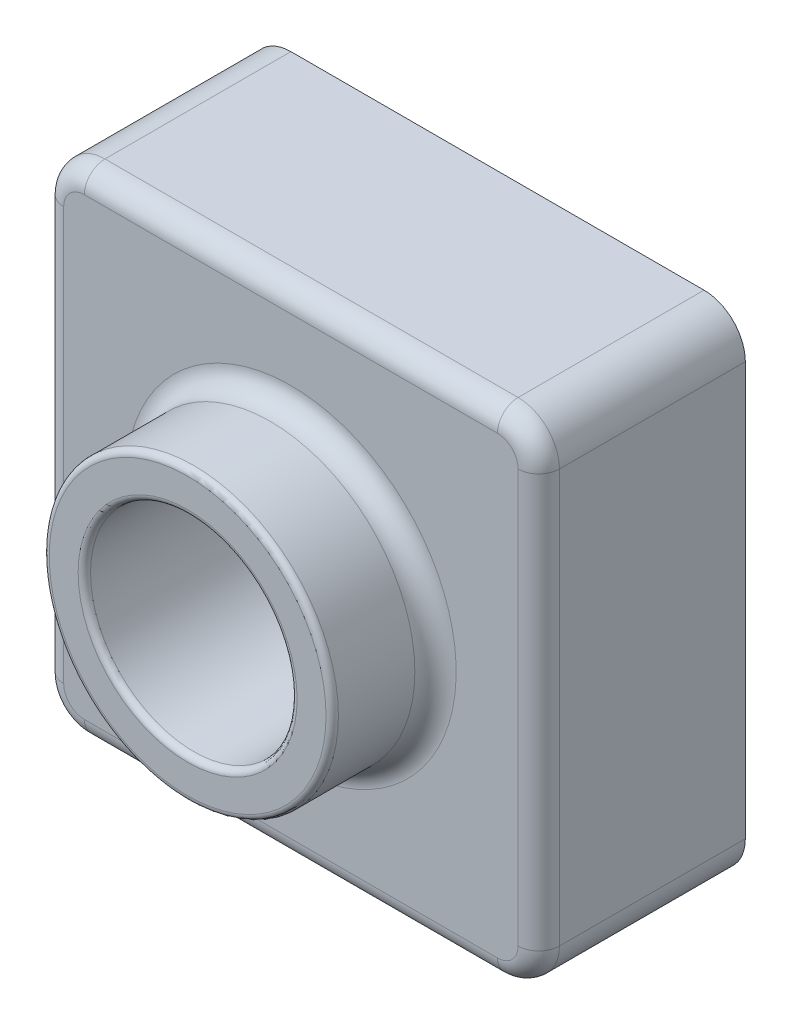
SolidWorks part; units mm, degrees
material "Chrome Stainless Steel"
ref_plane "Front Plane" through (0, 0, 0) normal (0, 0, 1) x (1, 0, 0)
ref_plane "Top Plane" through (0, 0, 0) normal (0, 1, 0) x (1, 0, 0)
ref_plane "Right Plane" through (0, 0, 0) normal (1, 0, 0) x (0, 0, -1)
sketch "Sketch2" plane through (0, 0, 0) normal (0, 0, 1) x (1, 0, 0)
  line L1 (0, 0) -> (120, 0)
  line L2 (0, 0) -> (0, 120)
  line L3 (0, 120) -> (120, 120)
  line L4 (120, 0) -> (120, 120)
  dimension "D1" = 120
  dimension "D2" = 120
extrude "Boss-Extrude2" add sketch "Sketch2" along normal blind 50
sketch "Sketch6" plane through (0, 0, 50) normal (0, 0, 1) x (1, 0, 0)
  line L0 (120, 120) -> (0, 120) construction
  line L1 (120, 0) -> (120, 120) construction
  circle A0 centre (60, 60) radius 35
  dimension "D1" = 70
  dimension "D2" = 60
  dimension "D3" = 60
extrude "Boss-Extrude3" add sketch "Sketch6" along normal blind 25
sketch "Sketch11" plane through (0, 0, 75) normal (0, 0, 1) x (1, 0, 0)
  circle A0 centre (60, 60) radius 25
  dimension "D1" = 50
extrude "Cut-Extrude1" cut sketch "Sketch11" against normal through all
fillet "Fillet3" radius 10 4 edges at (0, 0, 25) (0, 120, 25) (120, 0, 25) (120, 120, 25)
fillet "Fillet4" radius 1.5 2 edges at (95, 60, 75) (85, 60, 75)
fillet "Fillet5" radius 5 9 edges at (2.9289, 117.0711, 50) (60, 120, 50) (117.0711, 117.0711, 50) (120, 60, 50) (117.0711, 2.9289, 50) (60, 0, 50) (2.9289, 2.9289, 50) (0, 60, 50) (95, 60, 50)
shell "Shell2" thickness 2
